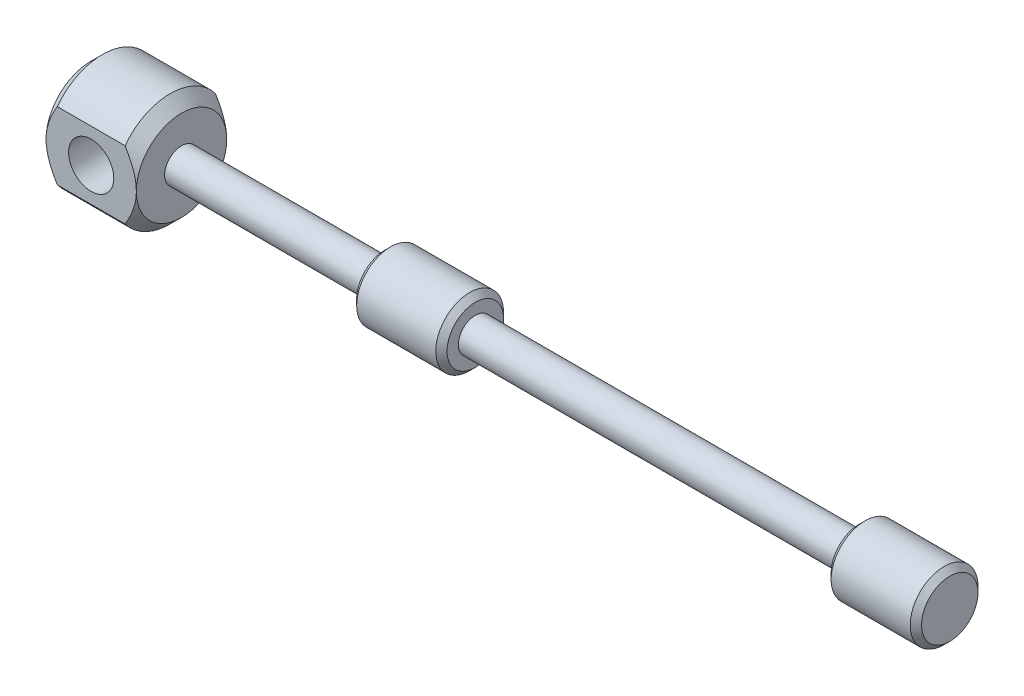
SolidWorks part; units mm, degrees
ref_plane "Front Plane" through (0, 0, 0) normal (0, 0, 1) x (1, 0, 0)
ref_plane "Top Plane" through (0, 0, 0) normal (0, 1, 0) x (1, 0, 0)
ref_plane "Right Plane" through (0, 0, 0) normal (1, 0, 0) x (0, 0, -1)
sketch "Sketch1" plane through (0, 0, 0) normal (1, 0, 0) x (0, 0, -1)
  circle A0 centre (0, 0) radius 1.5
extrude "Boss-Extrude1" add sketch "Sketch1" along normal blind 50
sketch "Sketch2" plane through (50, 0, 0) normal (1, 0, 0) x (0, 0, -1)
  circle A0 centre (0, 0) radius 3
extrude "Boss-Extrude2" add sketch "Sketch2" against normal blind 8
chamfer "Chamfer1" distance 0.5 angle 45 2 edges at (42, 0, -3) (50, 0, -3)
sketch "Sketch3" plane through (0, 0, 0) normal (-1, 0, 0) x (0, 0, 1)
  circle A1 centre (0, 0) radius 3
extrude "Boss-Extrude4" add sketch "Sketch3" against normal blind 8
chamfer "Chamfer2" distance 0.5 angle 45 2 edges at (8, 0, 3) (0, 0, 3)
sketch "Sketch5" plane through (0, 0, 0) normal (-1, 0, 0) x (0, 0, 1)
  circle A0 centre (0, 0) radius 1.5
extrude "Boss-Extrude5" add sketch "Sketch5" along normal blind 26
sketch "Sketch6" plane through (-26, 0, 0) normal (-1, 0, 0) x (0, 0, 1)
  circle A0 centre (0, 0) radius 5
extrude "Boss-Extrude6" add sketch "Sketch6" against normal blind 8
sketch "Sketch7" plane through (0, 0, 0) normal (0, 0, 1) x (1, 0, 0)
  circle A0 centre (-22, 0) radius 2
extrude "Cut-Extrude1" cut sketch "Sketch7" against normal through all both and the other way through all
chamfer "Chamfer3" distance 1 angle 45 2 edges at (-18, 0, 5) (-26, 0, 5)
sketch "Sketch8" plane through (-26, 0, 0) normal (-1, 0, 0) x (0, 0, 1)
  line L2 (-4, 4) -> (-4, -4)
  line L4 (4, 4) -> (4, -4)
  arc A0 (-4, 4) -> (-4, -4) centre (0, 0) ccw
  arc A1 (4, 4) -> (4, -4) centre (0, 0) cw
extrude "Cut-Extrude2" cut sketch "Sketch8" against normal through all both
